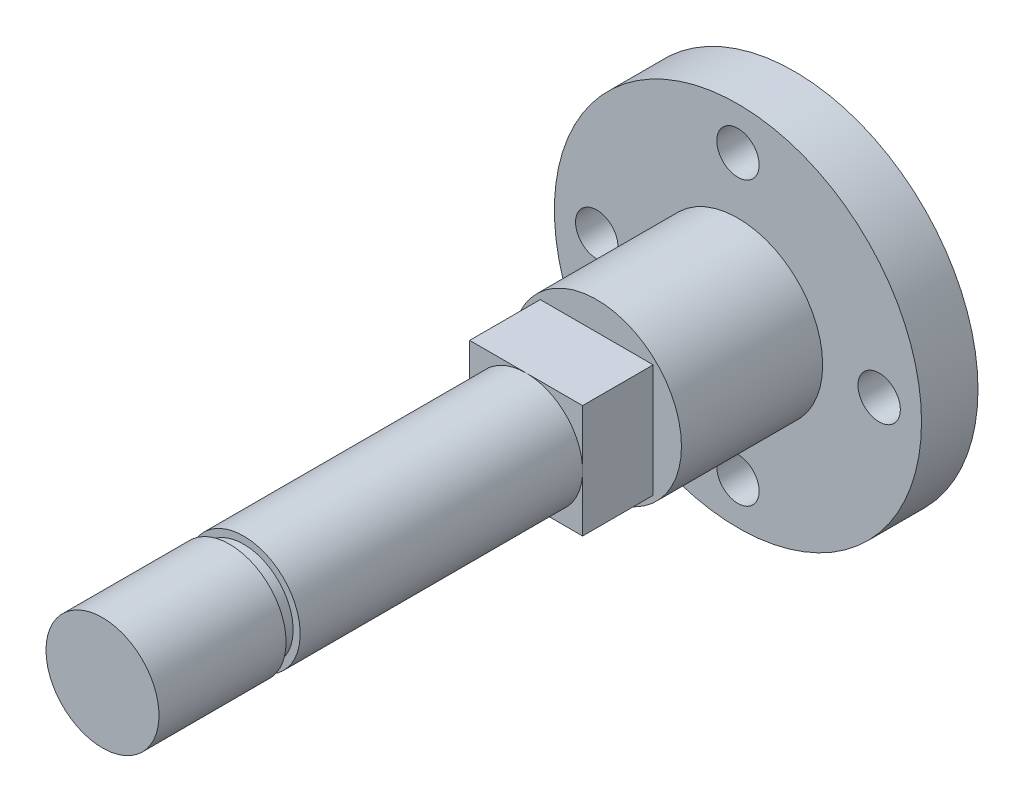
SolidWorks part; units mm, degrees
material "Plain Carbon Steel"
ref_plane "Front Plane" through (0, 0, 0) normal (0, 0, 1) x (1, 0, 0)
ref_plane "Top Plane" through (0, 0, 0) normal (0, 1, 0) x (1, 0, 0)
ref_plane "Right Plane" through (0, 0, 0) normal (1, 0, 0) x (0, 0, -1)
sketch "Sketch1" plane through (0, 0, 0) normal (0, 0, 1) x (1, 0, 0)
  circle A0 centre (0, 0) radius 13
  dimension "D1" = 26
extrude "Boss-Extrude1" add sketch "Sketch1" along normal blind 4
sketch "Sketch2" plane through (0, 0, 0) normal (0, 0, -1) x (-1, 0, 0)
  circle A0 centre (0, 0) radius 7.25
  dimension "D1" = 14.5
extrude "Cut-Extrude1" cut sketch "Sketch2" against normal blind 3
sketch "Sketch3" plane through (0, 0, 4) normal (0, 0, 1) x (1, 0, 0)
  circle A0 centre (0, 0) radius 10 construction
  circle A1 centre (0, 10) radius 1.5
  circle A2 centre (10, 0) radius 1.5
  circle A3 centre (0, -10) radius 1.5
  circle A4 centre (-10, 0) radius 1.5
  point P14 (0, 0)
  dimension "D1" = 20
  dimension "D2" = 3
  dimension "D3" = 4
extrude "Cut-Extrude2" cut sketch "Sketch3" against normal through all
sketch "Sketch6" plane through (0, 0, 4) normal (0, 0, 1) x (1, 0, 0)
  line L5 (4.2426, -4.2426) -> (-4.2426, -4.2426) construction
  line L7 (4.2426, -4.2426) -> (4.2426, 4.2426) construction
  line L8 (4.2426, 4.2426) -> (-4.2426, 4.2426) construction
  line L9 (-4.2426, -4.2426) -> (-4.2426, 4.2426) construction
  line L10 (4.2426, -4.2426) -> (-4.2426, 4.2426) construction
  line L11 (4.2426, 4.2426) -> (-4.2426, -4.2426) construction
  circle A1 centre (0, 0) radius 6
  circle A2 centre (-10, 0) radius 3.25 construction
  dimension "D1" = 12
  dimension "D2" = 6.5
extrude "Boss-Extrude5" add sketch "Sketch6" along normal blind 10
sketch "Sketch5" plane through (0, 0, 4) normal (0, 0, 1) x (1, 0, 0)
  line L0 (-4, 4) -> (0, 0) construction
  line L5 (-4, 4) -> (-4, -4)
  line L6 (-4, -4) -> (4, -4)
  line L13 (4, -4) -> (4, 4)
  line L14 (4, 4) -> (-4, 4)
  line L15 (0, 0) -> (4, -4) construction
  line L16 (4, 4) -> (0, 0) construction
  line L17 (0, 0) -> (-4, -4) construction
  circle A0 centre (0, 0) radius 4 construction
  dimension "D1" = 8
extrude "Boss-Extrude4" add sketch "Sketch5" along normal blind 5 from surface at 10 starting at face at (6, 0, 14)
sketch "Sketch4" plane through (0, 0, 4) normal (0, 0, 1) x (1, 0, 0)
  circle A0 centre (0, 0) radius 4
  dimension "D1" = 8
extrude "Boss-Extrude3" add sketch "Sketch4" along normal blind 30 from surface at 15 starting at face at (0, 0, 19)
sketch "Sketch8" plane through (0, 0, 0) normal (0, 1, 0) x (1, 0, 0)
  line L0 (-6, -14) -> (-6, -4)
  line L1 (-6, -4) -> (-13, -4)
  line L2 (-13, -4) -> (-6, -14)
  line L3 (0, 0) -> (0, -7.2893) construction
  line L4 (-6, -4) -> (-6, -14) construction
  line L5 (-6, -14) -> (6, -14) construction
revolve "Revolve1" [suppressed] add sketch "Sketch8" angle 360 about L3
sketch "Sketch9" plane through (0, 0, 4) normal (0, 0, 1) x (1, 0, 0)
  circle A0 centre (0, 0) radius 12.5
  dimension "D1" = 25
extrude "Boss-Extrude6" [suppressed] add sketch "Sketch9" along normal blind 5
sketch "Sketch7" plane through (0, 0, 14) normal (0, 0, 1) x (1, 0, 0)
  circle A0 centre (0, 0) radius 10 construction
  circle A1 centre (0, 10) radius 3
  circle A2 centre (10, 0) radius 3
  circle A3 centre (0, -10) radius 3
  circle A4 centre (-10, 0) radius 3
  point P17 (0, 0)
  dimension "D1" = 20
  dimension "D2" = 6
  dimension "D3" = 4
extrude "Cut-Extrude3" [suppressed] cut sketch "Sketch7" against normal blind 6
sketch "Sketch10" plane through (0, 0, 0) normal (0, 1, 0) x (1, 0, 0)
  line L6 (-5.5, -39) -> (-3.5, -39)
  line L9 (0, 0) -> (0, -49) construction
  line L10 (-4, -49) -> (4, -49) construction
  line L16 (-5.5, -39) -> (-5.5, -40)
  line L17 (-5.5, -40) -> (-3.5, -40)
  line L18 (-3.5, -39) -> (-3.5, -40)
  line L19 (-5.5, -39) -> (-3.5, -40) construction
  line L20 (-5.5, -40) -> (-3.5, -39) construction
  point P0 (-4.5, -39.5)
  dimension "D1" = 9
  dimension "D2" = 2
  dimension "D3" = 1
  dimension "D4" = 3.5
revolve "Cut-Revolve1" cut sketch "Sketch10" angle 360 about L9
ref_point "Point1" [suppressed]
sketch "Sketch11" plane through (0, 0, 0) normal (0, 1, 0) x (1, 0, 0)
  line L0 (-4, -19) -> (4, -19) construction
  line L1 (-3.5, -20) -> (-7.5, -20)
  line L2 (-3.5, -20) -> (-3.5, -19)
  line L3 (-3.5, -19) -> (-7.5, -19)
  line L4 (-7.5, -20) -> (-7.5, -19)
  line L5 (-3.5, -20) -> (-7.5, -19) construction
  line L6 (-3.5, -19) -> (-7.5, -20) construction
  line L7 (-4, -14) -> (4, -14) construction
  line L8 (0, -14) -> (0, -19) construction
  point P0 (-5.5, -19.5)
  dimension "D1" = 4
  dimension "D2" = 5
  dimension "D3" = 1
  dimension "D4" = 3.5
revolve "Cut-Revolve2" [suppressed] cut sketch "Sketch11" angle 360 about L8
fillet "Fillet1" [suppressed] radius 0.5
fillet "Fillet2" [suppressed] radius 0.1
